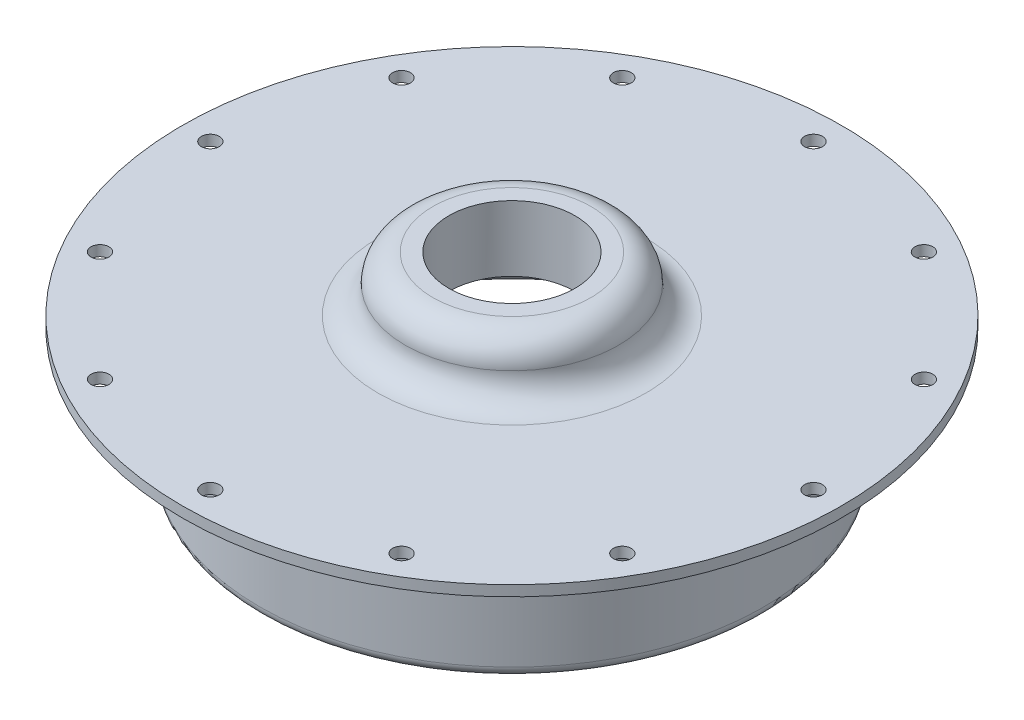
SolidWorks part; units mm, degrees
material "6063-T6"
ref_plane "Front Plane" through (0, 0, 0) normal (0, 0, 1) x (1, 0, 0)
ref_plane "Top Plane" through (0, 0, 0) normal (0, 1, 0) x (1, 0, 0)
ref_plane "Right Plane" through (0, 0, 0) normal (1, 0, 0) x (0, 0, -1)
ref_axis "Axis1" through (0, 55, 0) along (0, -1, 0)
sketch "Sketch1" plane through (0, 0, 0) normal (0, 0, 1) x (1, 0, 0)
  line L0 (-49.784, 0) -> (-39.6875, 0)
  line L1 (0, 55) -> (0, -55) construction
  line L2 (-49.784, 0) -> (-49.784, 1.5875)
  line L3 (-5.588, 9.906) -> (-11.938, 9.906)
  line L5 (-5.588, 9.906) -> (-5.588, 0)
  line L6 (-5.588, 0) -> (0, 0) construction
  line L7 (-49.784, 0) -> (-49.784, 1.5875) construction
  line L8 (-5.588, 1.5875) -> (-5.588, 0) construction
  line L9 (-38.1, -1.5875) -> (-38.1, -17.4625)
  line L11 (-34.925, -17.4625) -> (-34.925, -3.175)
  line L12 (-31.75, 0) -> (-5.588, 0)
  line L13 (0, -201000) -> (0, 249000) construction
  line L14 (-49.784, 1.5875) -> (-20.2565, 1.5875)
  arc A0 (-34.925, -3.175) -> (-31.75, 0) centre (-31.75, -3.175) cw
  arc A1 (-38.1, -1.5875) -> (-39.6875, 0) centre (-39.6875, -1.5875) ccw
  arc A2 (-20.2565, 1.5875) -> (-16.0972, 5.7467) centre (-20.2565, 5.7467) ccw
  arc A3 (-11.938, 9.906) -> (-16.0972, 5.7467) centre (-11.938, 5.7467) ccw
  arc A4 (-38.1, -17.4625) -> (-34.925, -17.4625) centre (-36.5125, -17.4625) ccw
  point P18 (-34.925, 0)
  dimension "D4" = 3.175
  dimension "D5" = 1.5875
  dimension "D1" = 3.175
  dimension "D2" = 38.1
  dimension "D3" = 17.4625
  dimension "D6" = 1.5875
  dimension "D7" = 6.35
  dimension "D8" = 9.906
revolve "Revolve1" add sketch "Sketch1" angle 360 about axis through (0, 55, 0) along (0, -1, 0)
ref_plane "Hole Location Plane" through (0, 3.175, 0) normal (0, 1, 0) x (1, 0, 0)
sketch "Hole Location" plane through (0, 3.175, 0) normal (0, 1, 0) x (1, 0, 0)
  line L0 (0, 0) -> (-45.5549, 0) construction
  circle A0 centre (0, 0) radius 45.5549 construction
  dimension "D1" = 91.1098
hole_wizard "#36 (0.1065) Diameter Hole1" positions "Sketch2" profile "Sketch3" hole size "#36" standard "ANSI Inch" end condition through all
sketch "Sketch2" plane through (0, 1.5875, 0) normal (0, 1, 0) x (1, 0, 0)
  point P0 (-45.5549, 0)
sketch "Sketch3" plane through (-45.5549, 1.5875, 0) normal (1, 0, 0) x (0, 0, 1)
  line L0 (0, 0) -> (0, 20.6375)
  line L1 (0, 20.6375) -> (1.3525, 20.6375)
  line L2 (1.3525, 20.6375) -> (1.3525, 0)
  line L5 (1.3525, 0) -> (0, 0)
  line L11 (0, -6.35) -> (0, 107.95) construction
  dimension "Thru Hole Dia." = 2.7051
  dimension "Thru Hole Depth" = 20.6375
pattern_circular "CirPattern1" count 12 over 360 about axis through (0, 0, 0) along (0, 1, 0) of "#36 (0.1065) Diameter Hole1"
hole_wizard "3/4 (0.75) Diameter Hole1" positions "Sketch5" profile "Sketch6" hole size "3/4" standard "ANSI Inch" end condition through all
sketch "Sketch5" plane through (0, 9.906, 0) normal (0, 1, 0) x (1, 0, 0)
  point P0 (0, 0)
sketch "Sketch6" plane through (0, 9.906, 0) normal (1, 0, 0) x (0, 0, 1)
  line L0 (0, 0) -> (0, 28.956)
  line L1 (0, 28.956) -> (9.525, 28.956)
  line L2 (9.525, 28.956) -> (9.525, 0)
  line L5 (9.525, 0) -> (0, 0)
  line L11 (0, -6.35) -> (0, 107.95) construction
  dimension "Thru Hole Dia." = 19.05
  dimension "Thru Hole Depth" = 28.956
equation "\"D1@Hole Location\"=\"TANK DIAMETER@Cryo Tank.Assembly\"+\"GASKET SEAT THICKNESS@Cryo Tank.Assembly\"+\"LINER THICKNESS@Cryo Tank.Assembly\"+\"SHRINK FIT DELTA@Cryo Tank.Assembly\""
equation "\"D2@Sketch1\"=\"TANK DIAMETER@Cryo Tank.Assembly\"/2"
equation "\"D3@Sketch1\"=0.5+0.125+0.0625"
